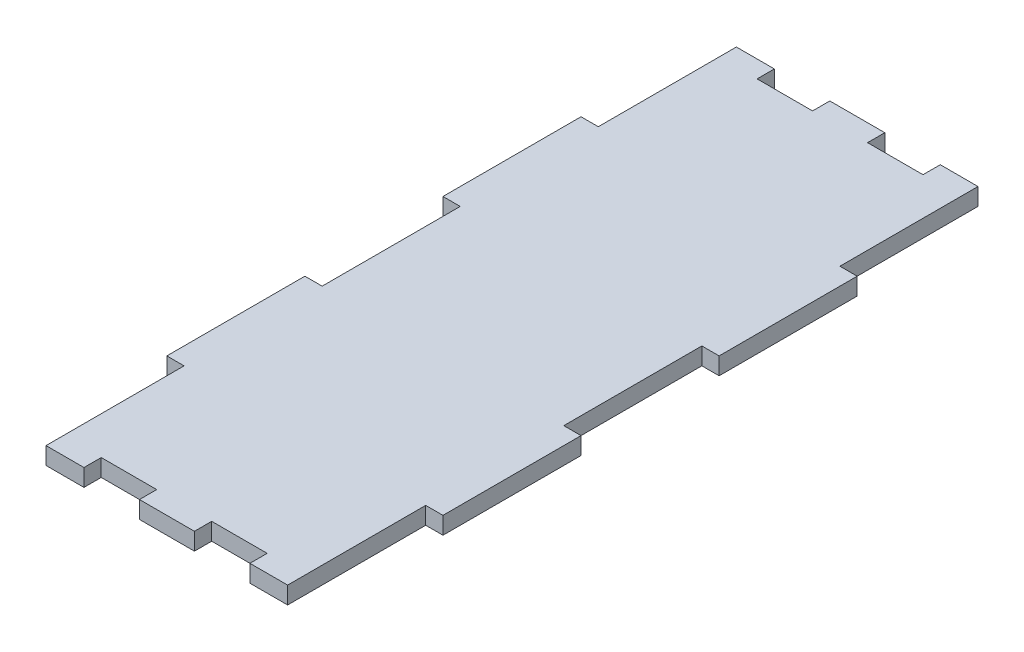
SolidWorks part; units mm, degrees
ref_plane "Front Plane" through (0, 0, 0) normal (0, 0, 1) x (1, 0, 0)
ref_plane "Top Plane" through (0, 0, 0) normal (0, 1, 0) x (1, 0, 0)
ref_plane "Right Plane" through (0, 0, 0) normal (1, 0, 0) x (0, 0, -1)
sketch "Sketch1" plane through (0, 0, 0) normal (0, 1, 0) x (1, 0, 0)
  line L1 (-25.4, -63.5) -> (25.4, -63.5)
  line L2 (-25.4, -63.5) -> (-25.4, 63.5)
  line L3 (-25.4, 63.5) -> (25.4, 63.5)
  line L4 (25.4, -63.5) -> (25.4, 63.5)
  line L5 (-25.4, -63.5) -> (25.4, 63.5) construction
  line L6 (-25.4, 63.5) -> (25.4, -63.5) construction
  point P0 (0, 0)
  dimension "D1" = 50.8
  dimension "D2" = 127
extrude "Boss-Extrude1" add sketch "Sketch1" along normal blind 3.175
sketch "Sketch2" plane through (0, 3.175, 0) normal (0, 1, 0) x (1, 0, 0)
  line L0 (-25.4, 63.5) -> (-25.4, -63.5) construction
  line L1 (-25.4, -12.7) -> (-22.225, -12.7)
  line L2 (-25.4, -12.7) -> (-25.4, 12.7)
  line L3 (-25.4, 12.7) -> (-22.225, 12.7)
  line L4 (-22.225, -12.7) -> (-22.225, 12.7)
  dimension "D1" = 25.4
  dimension "D2" = 3.175
  dimension "D3" = 50.8
extrude "Cut-Extrude1" cut sketch "Sketch2" against normal blind 3.175
pattern_linear "LPattern1" count 2 spacing 50.8 along (0, 0, -1) of "Cut-Extrude1"
pattern_linear "LPattern2" count 2 spacing 50.8 along (0, 0, 1) of "Cut-Extrude1"
sketch "Sketch3" plane through (0, 3.175, 0) normal (0, 1, 0) x (1, 0, 0)
  line L1 (25.4, 63.5) -> (22.225, 63.5)
  line L2 (25.4, 63.5) -> (25.4, 38.1)
  line L3 (25.4, 38.1) -> (22.225, 38.1)
  line L4 (22.225, 63.5) -> (22.225, 38.1)
  dimension "D1" = 25.4
  dimension "D2" = 3.175
extrude "Cut-Extrude2" cut sketch "Sketch3" against normal blind 3.175
pattern_linear "LPattern3" count 2 spacing 50.8 along (0, 0, 1) of "Cut-Extrude2"
pattern_linear "LPattern4" count 2 spacing 50.8 along (0, 0, 1) of "LPattern3"
ref_plane "Plane1" through (-25.4, 3.175, -38.1) normal (0, 0, 1) x (1, 0, 0)
sketch "Sketch5" plane through (0, 3.175, 0) normal (0, 1, 0) x (1, 0, 0)
  line L0 (-25.4, -19.1687) -> (-25.4, -58.0313) construction
  line L2 (25.4, 24.4204) -> (25.4, 49.9787) construction
  line L3 (5.08, 63.5) -> (-5.08, 63.5)
  line L4 (-7.174, 63.5) -> (16.1086, 63.5) construction
  line L5 (5.08, 63.5) -> (5.08, 60.325)
  line L6 (-22.225, -63.5) -> (28.3592, -63.5) construction
  line L7 (5.08, 60.325) -> (-5.08, 60.325)
  line L8 (-5.08, 63.5) -> (-5.08, 60.325)
  line L9 (-5.08, -63.5) -> (5.08, -63.5)
  line L10 (-5.08, -63.5) -> (-5.08, -60.325)
  line L11 (-5.08, -60.325) -> (5.08, -60.325)
  line L12 (5.08, -63.5) -> (5.08, -60.325)
  dimension "D1" = 10.16
  dimension "D2" = 20.32
  dimension "D3" = 3.175
  dimension "D4" = 3.175
  dimension "D5" = 10.16
ref_plane "Plane2" through (-22.225, 3.175, -63.5) normal (-1, 0, 0) x (0, 0, 1)
sketch "Sketch6" plane through (0, 3.175, 0) normal (0, 1, 0) x (1, 0, 0)
  line L0 (-200007.174, 63.5) -> (200016.1086, 63.5) construction
  line L1 (5.08, 60.325) -> (15.2856, 60.325)
  line L2 (5.08, 60.325) -> (5.08, 63.5)
  line L3 (5.08, 63.5) -> (15.2856, 63.5)
  line L4 (15.2856, 60.325) -> (15.2856, 63.5)
  line L6 (5.08, -63.5) -> (15.2856, -63.5)
  line L7 (5.08, -63.5) -> (5.08, -60.325)
  line L8 (5.08, -60.325) -> (15.2856, -60.325)
  line L9 (15.2856, -63.5) -> (15.2856, -60.325)
  dimension "D1" = 10.2056
  dimension "D2" = 3.175
extrude "Cut-Extrude3" cut sketch "Sketch6" against normal blind 3.175
pattern_linear "LPattern5" count 2 spacing 20.32 along (-1, 0, 0) of "Cut-Extrude3"
